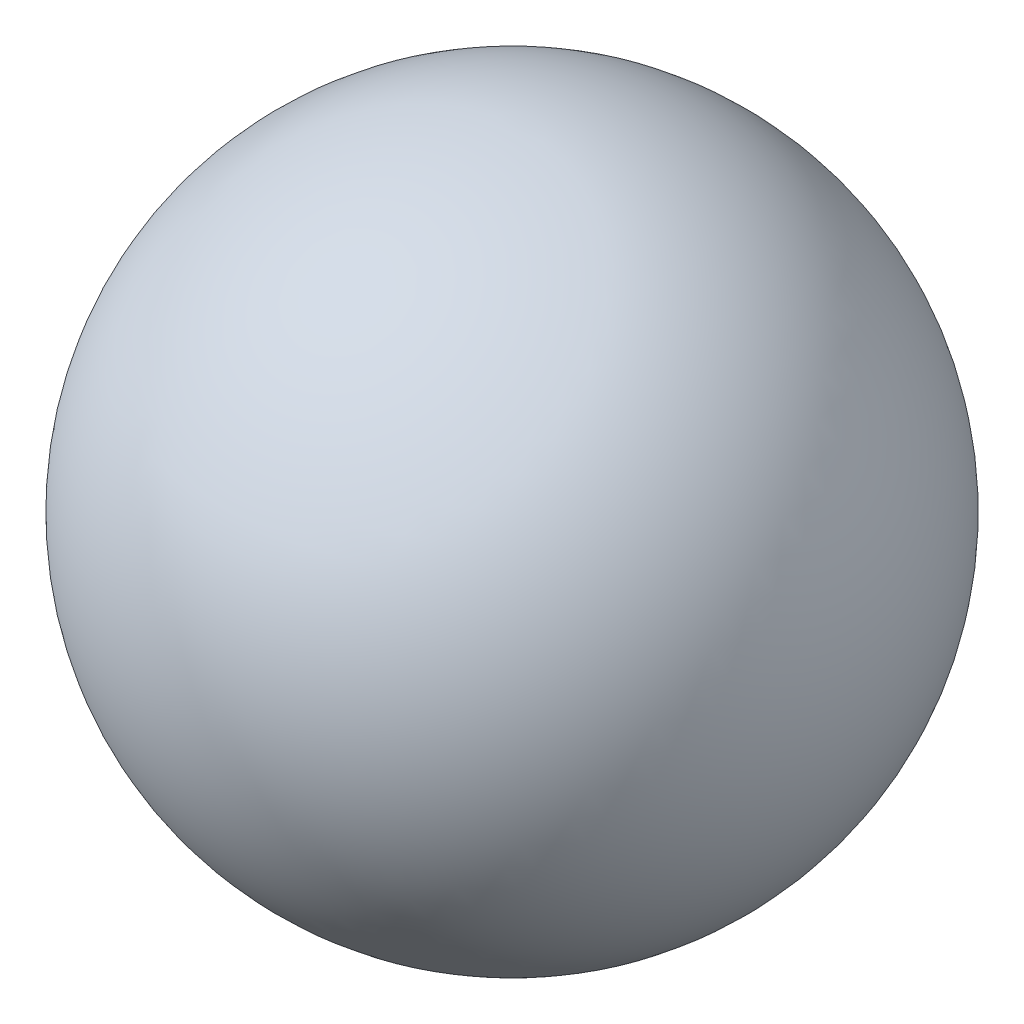
SolidWorks part; units mm, degrees
ref_plane "Ön Düzlem" through (0, 0, 0) normal (0, 0, 1) x (1, 0, 0)
ref_plane "Üst Düzlem" through (0, 0, 0) normal (0, 1, 0) x (1, 0, 0)
ref_plane "Sağ Düzlem" through (0, 0, 0) normal (1, 0, 0) x (0, 0, -1)
sketch "Çizim1" plane through (0, 0, 0) normal (0, 0, 1) x (1, 0, 0)
  line L0 (0, 30) -> (0, -30)
  arc A0 (0, -30) -> (0, 30) centre (0, 0) ccw
  dimension "D1" = 60
revolve "Döndür1" add sketch "Çizim1" angle 360 about L0
